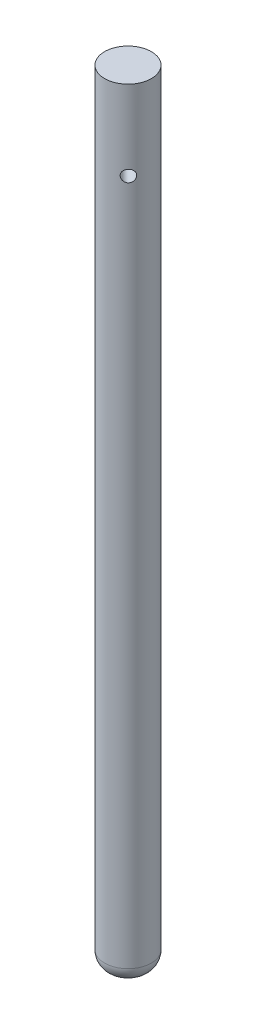
SolidWorks part; units mm, degrees
ref_plane "Front Plane" through (0, 0, 0) normal (0, 0, 1) x (1, 0, 0)
ref_plane "Top Plane" through (0, 0, 0) normal (0, 1, 0) x (1, 0, 0)
ref_plane "Right Plane" through (0, 0, 0) normal (1, 0, 0) x (0, 0, -1)
sketch "Sketch1" plane through (0, 0, 0) normal (0, 1, 0) x (1, 0, 0)
  circle A0 centre (0, 0) radius 2.99
extrude "Boss-Extrude1" add sketch "Sketch1" along normal blind 100
sketch "Sketch2" plane through (0, 100, 0) normal (0, 1, 0) x (1, 0, 0)
  point P0 (0, 0)
ref_plane "Plane1" through (0, 0, 12.54) normal (0, 0, 1) x (1, 0, 0)
sketch "Sketch3" plane through (0, 0, 12.54) normal (0, 0, 1) x (1, 0, 0)
  point P0 (0, 90)
  dimension "D1" = 10
hole_wizard "Ø1.5mm Dowel Hole5" positions "3DSketch4" profile "Sketch7" hole size "Ø1.5" standard "ANSI Metric"
sketch3d "3DSketch4"
  point P0 (2.1442, 89.8183, 2.0838)
sketch "Sketch7" plane through (2.1442, 89.8183, 2.0838) normal (0, 1, 0) x (0.6969, 0, -0.7171)
  line L0 (0, 0) -> (0, 20.4506)
  line L1 (0, 20.4506) -> (0.75, 20)
  line L2 (0.75, 20) -> (0.75, 0)
  line L5 (0.75, 0) -> (0, 0)
  line L10 (0, 20.4506) -> (-0.75, 20) construction
  line L11 (0, -6.35) -> (0, 107.95) construction
  dimension "Hole Dia." = 1.5
  dimension "Hole Depth" = 20
  dimension "Drill Angle" = 118
fillet "Fillet1" radius 2 1 edges at (0, 0, 2.99)
